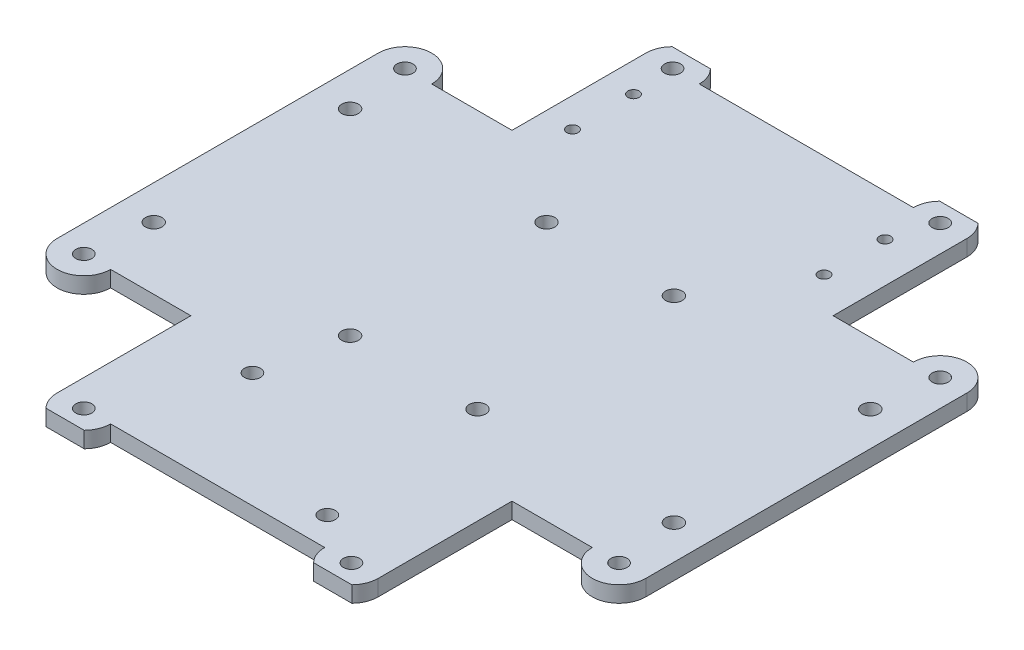
SolidWorks part; units mm, degrees
ref_plane "Front Plane" through (0, 0, 0) normal (0, 0, 1) x (1, 0, 0)
ref_plane "Top Plane" through (0, 0, 0) normal (0, 1, 0) x (1, 0, 0)
ref_plane "Right Plane" through (0, 0, 0) normal (1, 0, 0) x (0, 0, -1)
sketch "Sketch1" plane through (0, 0, 0) normal (0, 1, 0) x (1, 0, 0)
  line L0 (-55, 0) -> (55, 0) construction
  line L1 (55, -55) -> (-55, -55)
  line L2 (55, -55) -> (55, 55)
  line L3 (55, 55) -> (-55, 55)
  line L4 (-55, -55) -> (-55, 55)
  line L5 (55, -55) -> (-55, 55) construction
  line L6 (55, 55) -> (-55, -55) construction
  line L7 (-8.5, -21.75) -> (-52, -21.75)
  line L8 (-8.5, -21.75) -> (-8.5, 21.75)
  line L9 (-8.5, 21.75) -> (-52, 21.75)
  line L10 (-52, -21.75) -> (-52, 21.75)
  line L11 (-8.5, -21.75) -> (-52, 21.75) construction
  line L12 (-8.5, 21.75) -> (-52, -21.75) construction
  line L13 (0, -55) -> (0, 55) construction
  line L14 (8.5, 21.75) -> (52, 21.75)
  line L15 (52, -21.75) -> (52, 21.75)
  line L16 (8.5, -21.75) -> (52, -21.75)
  line L17 (8.5, -21.75) -> (8.5, 21.75)
  line L18 (0, 55) -> (0, -55) construction
  line L19 (-26.5, 52) -> (26.5, 52)
  line L20 (-26.5, 52) -> (-26.5, 31)
  line L21 (-26.5, 31) -> (26.5, 31)
  line L22 (26.5, 52) -> (26.5, 31)
  line L24 (-22, -31) -> (22, -31)
  line L25 (-22, -31) -> (-22, -52)
  line L26 (-22, -52) -> (22, -52)
  line L27 (22, -31) -> (22, -52)
  line L28 (-22, -31) -> (22, -52) construction
  line L29 (-22, -52) -> (22, -31) construction
  circle A0 centre (-48.6, 18.35) radius 1.55
  circle A1 centre (-11.9, 18.35) radius 1.55
  circle A2 centre (-11.9, -18.35) radius 1.55
  circle A3 centre (-48.6, -18.35) radius 1.55
  circle A4 centre (48.6, -18.35) radius 1.55
  circle A5 centre (11.9, -18.35) radius 1.55
  circle A6 centre (11.9, 18.35) radius 1.55
  circle A7 centre (48.6, 18.35) radius 1.55
  circle A8 centre (-24.5, 47.2) radius 1.05
  circle A9 centre (-24.5, 35.8) radius 1.05
  circle A10 centre (22.5, 47.2) radius 1.05
  circle A11 centre (22.5, 35.8) radius 1.05
  circle A12 centre (-15, -33.5) radius 1.5
  circle A13 centre (15, -49.5) radius 1.5
  point P0 (0, 0)
  point P6 (-30.25, 0)
  point P25 (0, 52)
  point P26 (0, -41.5)
  dimension "D12" = 3.1
  dimension "D15" = 2.1
  dimension "D20" = 2.1
  dimension "D21" = 2.1
  dimension "D24" = 2.1
  dimension "D29" = 3
  dimension "D32" = 3
  dimension "D1" = 110
  dimension "D2" = 110
  dimension "D3" = 43.5
  dimension "D4" = 43.5
  dimension "D5" = 3
  dimension "D6" = 21
  dimension "D7" = 53
  dimension "D8" = 3
  dimension "D9" = 21
  dimension "D10" = 44
  dimension "D11" = 3
  dimension "D13" = 3.4
  dimension "D16" = 2
  dimension "D17" = 4.8
  dimension "D18" = 2
  dimension "D19" = 4.8
  dimension "D22" = 4.8
  dimension "D23" = 4.8
  dimension "D25" = 49
  dimension "D26" = 49
  dimension "D27" = 2.5
  dimension "D28" = 7
  dimension "D30" = 2.5
  dimension "D31" = 7
  dimension "D14" = 4
extrude "Boss-Extrude2" add sketch "Sketch1" along normal blind 3 contours L2 L1 L4 L3 | A4 | A7 | A11 | A10 | A8 | A9 | A3 | A0 | A1 | A2 | A5 | A6 | A12 | A13
sketch "Sketch3" plane through (0, 3, 0) normal (0, 1, 0) x (1, 0, 0)
  line L0 (55, 55) -> (30, 55)
  line L1 (-55, 55) -> (-30, 55)
  line L2 (-55, 55) -> (-55, 30)
  line L3 (-55, 30) -> (-30, 30)
  line L4 (-30, 55) -> (-30, 30)
  line L5 (55, 55) -> (55, 30)
  line L6 (55, 30) -> (30, 30)
  line L7 (30, 55) -> (30, 30)
  line L8 (55, -55) -> (55, -30)
  line L9 (55, -55) -> (30, -55)
  line L10 (30, -55) -> (30, -30)
  line L11 (55, -30) -> (30, -30)
  line L12 (-55, -55) -> (-30, -55)
  line L13 (-55, -55) -> (-55, -30)
  line L14 (-55, -30) -> (-30, -30)
  line L15 (-30, -55) -> (-30, -30)
  point P20 (0, 0)
  dimension "D1" = 25
  dimension "D2" = 25
  dimension "D3" = 4
extrude "Cut-Extrude1" cut sketch "Sketch3" against normal blind 3
sketch "Sketch4" plane through (0, 3, 0) normal (0, 1, 0) x (1, 0, 0)
  line L0 (30, 30) -> (55, 30) construction
  line L1 (55, -30) -> (55, 30) construction
  line L3 (0, -1.65) -> (0, 1.65) construction
  line L4 (-1.65, 0) -> (1.65, 0) construction
  line L5 (30, 55) -> (-30, 55) construction
  line L6 (-30, 30) -> (-30, 55) construction
  circle A0 centre (50, 30) radius 5
  circle A4 centre (-50, 30) radius 5
  circle A5 centre (50, -30) radius 5
  circle A6 centre (-50, -30) radius 5
  circle A7 centre (-25, 55) radius 5
  circle A8 centre (25, 55) radius 5
  circle A9 centre (25, -55) radius 5
  circle A10 centre (-25, -55) radius 5
  point P12 (2.5304, -17.4696)
  dimension "D1" = 10
  dimension "D2" = 10
extrude "Boss-Extrude3" add sketch "Sketch4" against normal up to surface (3 mm away) up to face at (0, 0, 0)
sketch "Sketch5" plane through (0, 3, 0) normal (0, 1, 0) x (1, 0, 0)
  line L0 (-1.65, 0) -> (1.65, 0) construction
  line L1 (0, -1.65) -> (0, 1.65) construction
  circle A0 centre (50, 30) radius 1.5
  circle A5 centre (50, -30) radius 1.5
  circle A6 centre (-50, -30) radius 1.5
  circle A7 centre (-50, 30) radius 1.5
  circle A8 centre (-25, 55) radius 1.5
  circle A9 centre (25, 55) radius 1.5
  circle A10 centre (25, -55) radius 1.5
  circle A11 centre (-25, -55) radius 1.5
  dimension "D1" = 3
  dimension "D2" = 3
extrude "Cut-Extrude3" cut sketch "Sketch5" against normal through all
sketch "Sketch6" plane through (0, 3, 0) normal (0, 1, 0) x (1, 0, 0)
  line L0 (-30, 55) -> (-30, 58.5) construction
  line L1 (30, 55) -> (30, 30) construction
  line L2 (-30, 58.5) -> (30, 58.5)
  line L3 (-30, 58.5) -> (-30, 60)
  line L4 (-30, 60) -> (30, 60)
  line L5 (30, 58.5) -> (30, 60)
  line L6 (-1.65, 0) -> (1.65, 0) construction
  line L7 (-30, -60) -> (30, -60)
  line L8 (30, -58.5) -> (30, -60)
  line L9 (-30, -58.5) -> (30, -58.5)
  line L10 (-30, -58.5) -> (-30, -60)
  arc A0 (30, 55) -> (20, 55) centre (25, 55) ccw construction
  dimension "D1" = 3.5
extrude "Cut-Extrude6" cut sketch "Sketch6" along normal through all both and the other way through all contours L3 L2 L5 L4 | L7 L8 L9 L10
